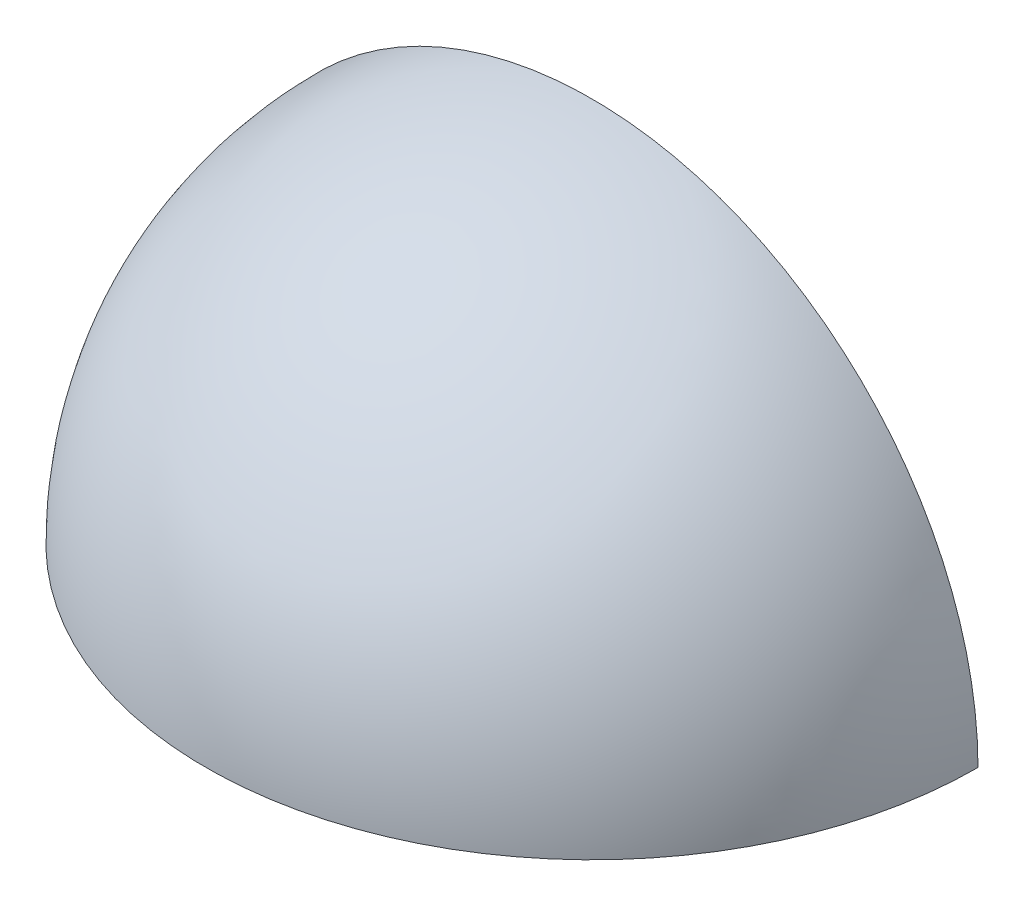
SolidWorks part; units mm, degrees
material "PET"
ref_plane "Alzado" through (0, 0, 0) normal (0, 0, 1) x (1, 0, 0)
ref_plane "Planta" through (0, 0, 0) normal (0, 1, 0) x (1, 0, 0)
ref_plane "Vista lateral" through (0, 0, 0) normal (1, 0, 0) x (0, 0, -1)
sketch "Croquis1" plane through (0, 0, 0) normal (0, 0, 1) x (1, 0, 0)
  line L0 (-30, 0) -> (30, 0) construction
  line L1 (-30, 0) -> (-28.5, 0)
  line L2 (28.5, 0) -> (30, 0)
  arc A0 (30, 0) -> (-30, 0) centre (0, 0) ccw
  arc A1 (28.5, 0) -> (-28.5, 0) centre (0, 0) ccw
  dimension "D1" = 60
  dimension "D2" = 1.5
revolve "Revolución1" add sketch "Croquis1" angle 90 about L0
